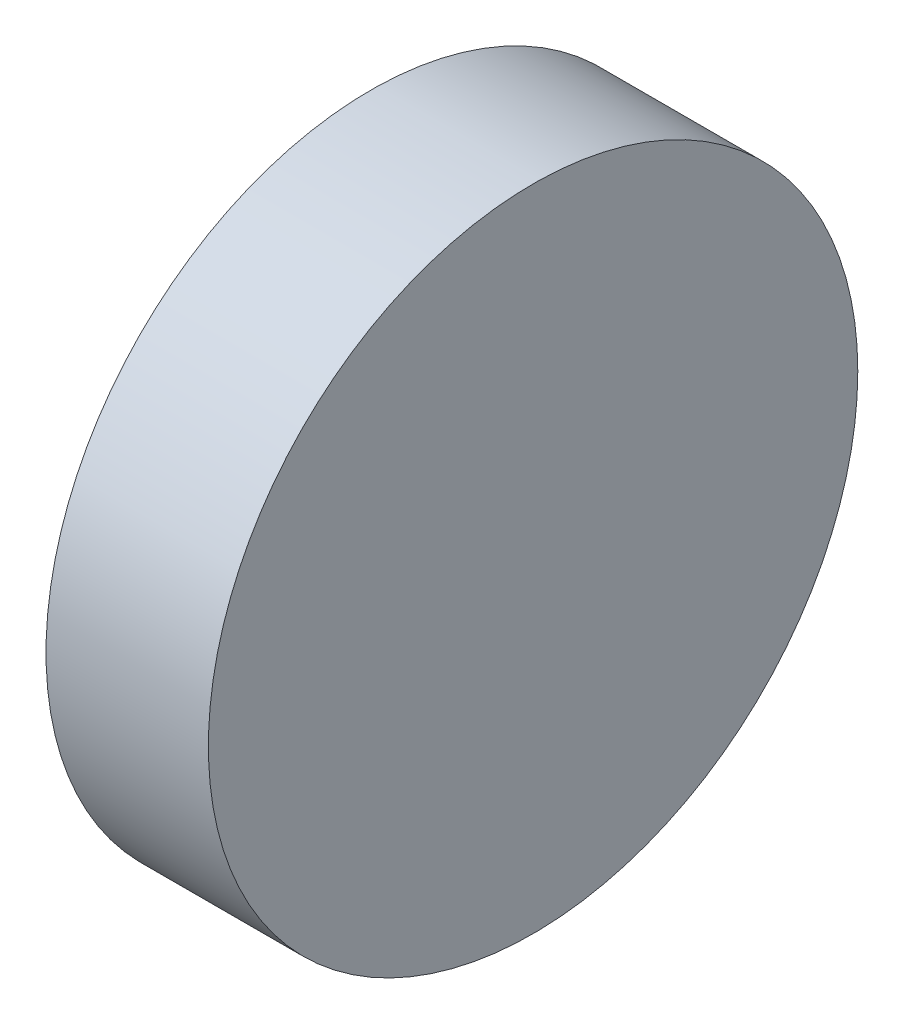
SolidWorks part; units mm, degrees
ref_plane "Front Plane" through (0, 0, 0) normal (0, 0, 1) x (1, 0, 0)
ref_plane "Top Plane" through (0, 0, 0) normal (0, 1, 0) x (1, 0, 0)
ref_plane "Right Plane" through (0, 0, 0) normal (1, 0, 0) x (0, 0, -1)
sketch "Sketch2" plane through (0, 0, 0) normal (1, 0, 0) x (0, 0, -1)
  circle A0 centre (0, 0) radius 20
extrude "Boss-Extrude1" add sketch "Sketch2" along normal blind 10
